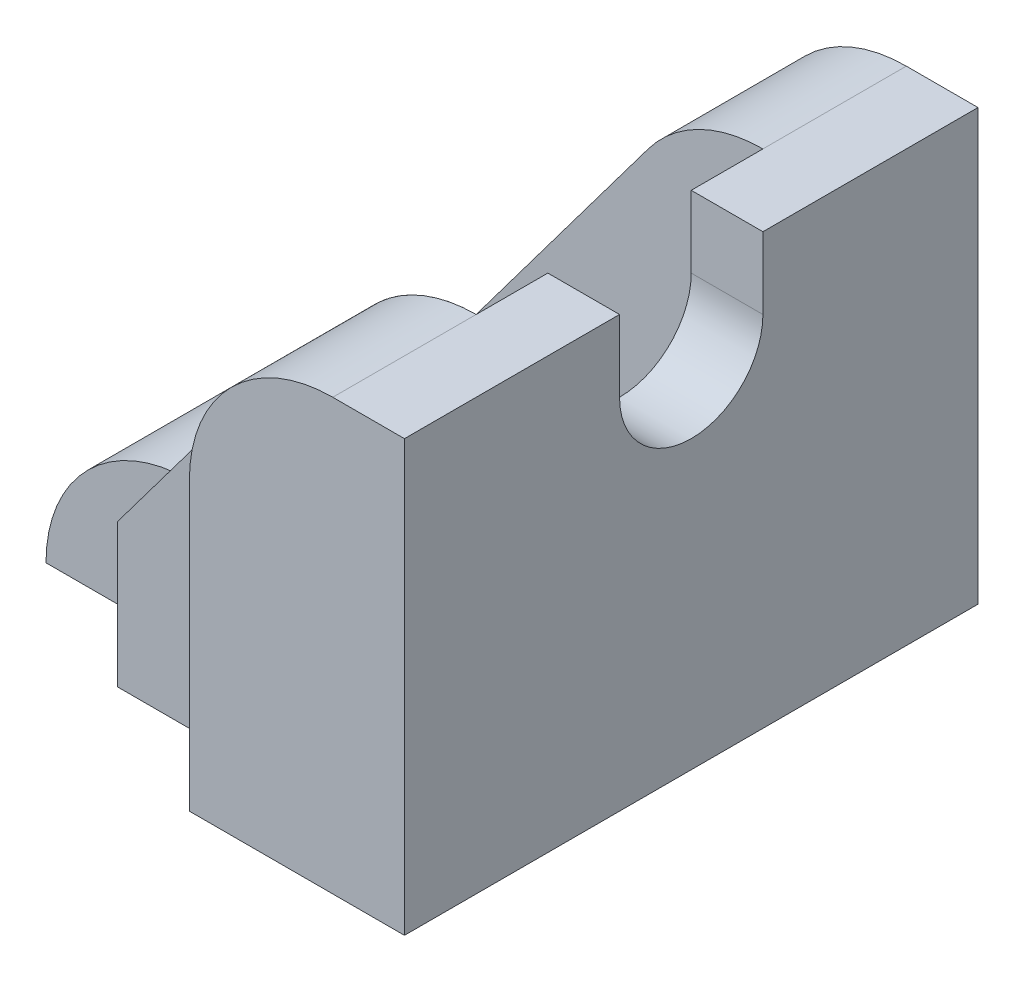
SolidWorks part; units mm, degrees
ref_plane "Front Plane" through (0, 0, 0) normal (0, 0, 1) x (1, 0, 0)
ref_plane "Top Plane" through (0, 0, 0) normal (0, 1, 0) x (1, 0, 0)
ref_plane "Right Plane" through (0, 0, 0) normal (1, 0, 0) x (0, 0, -1)
sketch "Sketch1" plane through (0, 0, 0) normal (0, 0, 1) x (1, 0, 0)
  line L0 (0, 0) -> (-3, 0)
  line L2 (0, 0) -> (0, 6)
  line L3 (-3, 0) -> (-5, 0)
  line L4 (-5, 0) -> (-5, 2)
  line L5 (0, 6) -> (-1, 6)
  line L6 (-2.6, 5.2) -> (-5, 2)
  arc A0 (-1, 6) -> (-2.6, 5.2) centre (-1, 4) ccw
  dimension "D4" = 2
  dimension "D1" = 3
  dimension "D2" = 2
  dimension "D3" = 6
  dimension "D5" = 2
  dimension "D6" = 1
extrude "Boss-Extrude1" add sketch "Sketch1" along normal blind 8
sketch "Sketch2" plane through (0, 6, 0) normal (0, 1, 0) x (1, 0, 0)
  line L0 (-1, -2) -> (-1, -6)
  line L1 (-1, -8) -> (-1, 0) construction
  line L2 (-1, -6) -> (-5, -6)
  line L3 (-5, -8) -> (-5, 0) construction
  line L4 (-5, -6) -> (-5, -2)
  line L5 (-5, -2) -> (-1, -2)
  dimension "D1" = 2
  dimension "D2" = 2
extrude "Cut-Extrude1" cut sketch "Sketch2" against normal blind 4
sketch "Sketch3" plane through (-1, 0, 0) normal (-1, 0, 0) x (0, 0, 1)
  line L0 (3, 6) -> (3, 5)
  line L1 (6, 6) -> (2, 6) construction
  line L2 (5, 6) -> (5, 5)
  line L3 (5, 6) -> (3, 6)
  arc A0 (3, 5) -> (5, 5) centre (4, 5) ccw
  dimension "D3" = 3
  dimension "D1" = 1
  dimension "D2" = 1
extrude "Cut-Extrude2" cut sketch "Sketch3" against normal through all
sketch "Sketch5" plane through (0, 0, 8) normal (0, 0, 1) x (1, 0, 0)
  line L0 (-5, 0) -> (-7, 0)
  line L1 (-5, 2) -> (-5, 0)
  arc A0 (-5, 2) -> (-7, 0) centre (-5, 0) ccw
  dimension "D2" = 2
  dimension "D1" = 2
extrude "Boss-Extrude2" add sketch "Sketch5" against normal blind 6
sketch "Sketch6" plane through (0, 0, 8) normal (0, 0, 1) x (1, 0, 0)
  line L0 (-5, 2) -> (-5, 0)
  line L1 (-5, 0) -> (-7, 0)
  arc A0 (-5, 2) -> (-7, 0) centre (-5, 0) ccw
  arc A1 (-5, 2) -> (-7, 0) centre (-5, 0) ccw construction
extrude "Cut-Extrude4" cut sketch "Sketch6" against normal blind 2
sketch "Sketch7" plane through (0, 2, 0) normal (0, 1, 0) x (1, 0, 0)
  line L0 (-4, -4) -> (-3, -4) construction
  line L1 (-4, -3) -> (-3, -3)
  line L2 (-4, -5) -> (-3, -5)
  line L3 (-5, -2) -> (-5, -6) construction
  line L4 (-1, -2) -> (-5, -2) construction
  arc A0 (-4, -3) -> (-4, -5) centre (-4, -4) ccw
  arc A1 (-3, -5) -> (-3, -3) centre (-3, -4) ccw
  point P2 (-3.5, -4)
  point P7 (-5, -4)
  dimension "D1" = 1
  dimension "D2" = 1
  dimension "D3" = 1
  dimension "D4" = 1
extrude "Cut-Extrude5" cut sketch "Sketch7" against normal through all
sketch "Sketch8" plane through (0, 0, 8) normal (0, 0, 1) x (1, 0, 0)
  line L0 (-5, 0) -> (-3, 0)
  line L1 (-5, 0) -> (0, 0) construction
  line L2 (-3, 0) -> (-3, 4)
  line L4 (-5, 2) -> (-5, 0)
  line L5 (-5, 2) -> (-2.6, 5.2)
  arc A0 (-3, 4) -> (-2.6, 5.2) centre (-1, 4) cw
  dimension "D1" = 2
extrude "Cut-Extrude8" cut sketch "Sketch8" against normal blind 1
sketch "Sketch9" plane through (0, 0, 0) normal (0, 0, -1) x (-1, 0, 0)
  line L0 (5, 0) -> (5, 2)
  line L1 (5, 0) -> (3, 0)
  line L2 (5, 0) -> (0, 0) construction
  line L3 (3, 0) -> (3, 4)
  line L4 (5, 2) -> (2.6, 5.2)
  line L5 (2.6, 5.2) -> (5, 2) construction
  arc A0 (2.6, 5.2) -> (3, 4) centre (1, 4) cw
  dimension "D1" = 2
  dimension "D2" = 4
extrude "Cut-Extrude9" cut sketch "Sketch9" against normal blind 1
